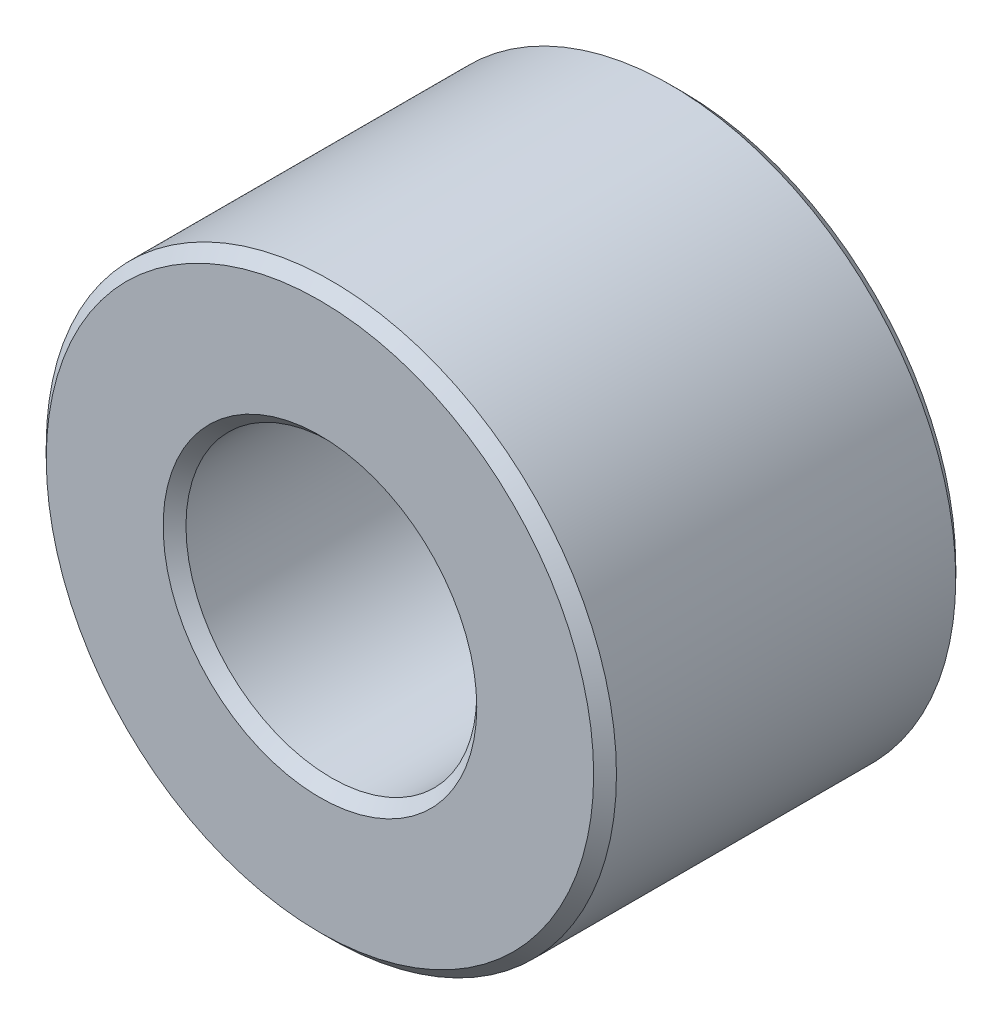
SolidWorks part; units mm, degrees
material "6061-T6 (SS)"
ref_plane "Front Plane" through (0, 0, 0) normal (0, 0, 1) x (1, 0, 0)
ref_plane "Top Plane" through (0, 0, 0) normal (0, 1, 0) x (1, 0, 0)
ref_plane "Right Plane" through (0, 0, 0) normal (1, 0, 0) x (0, 0, -1)
sketch "Sketch1" plane through (0, 0, 0) normal (0, 0, 1) x (1, 0, 0)
  circle A0 centre (0, 0) radius 2.55
  circle A1 centre (0, 0) radius 5
  dimension "D1" = 5.1
  dimension "D2" = 10
extrude "Boss-Extrude1" add sketch "Sketch1" along normal blind 6.35
chamfer "Chamfer1" distance 0.2 angle 45 4 edges at (5, 0, 0) (2.55, 0, 0) (2.55, 0, 6.35) (5, 0, 6.35)
